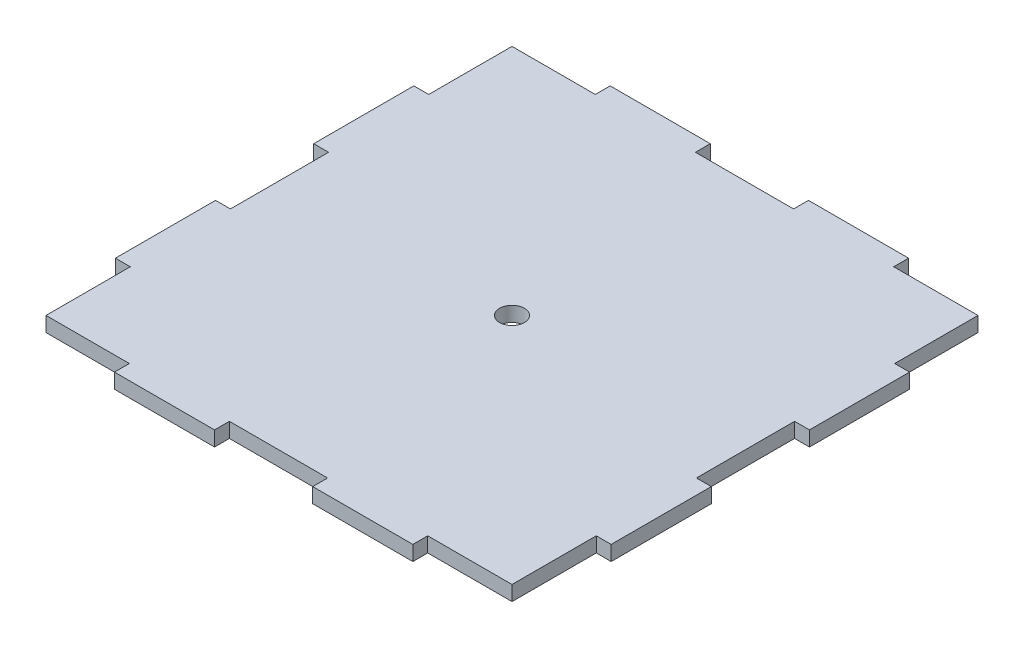
SolidWorks part; units mm, degrees
ref_plane "Front Plane" through (0, 0, 0) normal (0, 0, 1) x (1, 0, 0)
ref_plane "Top Plane" through (0, 0, 0) normal (0, 1, 0) x (1, 0, 0)
ref_plane "Right Plane" through (0, 0, 0) normal (1, 0, 0) x (0, 0, -1)
sketch "Sketch1" plane through (0, 0, 0) normal (0, 1, 0) x (1, 0, 0)
  line L0 (40, 97) -> (40, 100)
  line L1 (0, 0) -> (100, 0)
  line L2 (0, 0) -> (0, 100)
  line L3 (0, 100) -> (100, 100)
  line L4 (100, 0) -> (100, 100)
  line L9 (0, 97) -> (19.8, 97)
  line L10 (0, 97) -> (0, 100)
  line L11 (0, 100) -> (19.8, 100)
  line L12 (19.8, 97) -> (19.8, 100)
  line L13 (40, 97) -> (59.8, 97)
  line L14 (59.8, 97) -> (59.8, 100)
  line L15 (40, 100) -> (59.8, 100)
  line L16 (80, 97) -> (80, 100)
  line L17 (80, 97) -> (99.8, 97)
  line L18 (99.8, 97) -> (99.8, 100)
  line L19 (80, 100) -> (99.8, 100)
  line L20 (3, 60) -> (3, 40.2)
  line L21 (3, 100) -> (0, 100)
  line L22 (3, 100) -> (3, 80.2)
  line L23 (3, 80.2) -> (0, 80.2)
  line L24 (0, 100) -> (0, 80.2)
  line L25 (3, 60) -> (0, 60)
  line L26 (0, 60) -> (0, 40.2)
  line L27 (3, 40.2) -> (0, 40.2)
  line L28 (3, 20) -> (3, 0.2)
  line L29 (3, 20) -> (0, 20)
  line L30 (0, 20) -> (0, 0.2)
  line L31 (3, 0.2) -> (0, 0.2)
  line L32 (-900, 50) -> (49100, 50) construction
  line L33 (50, -900) -> (50, 49100) construction
  line L34 (80, 3) -> (99.8, 3)
  line L35 (99.8, 3) -> (99.8, 0)
  line L36 (80, 0) -> (99.8, 0)
  line L37 (80, 3) -> (80, 0)
  line L38 (40, 3) -> (59.8, 3)
  line L39 (59.8, 3) -> (59.8, 0)
  line L40 (40, 0) -> (59.8, 0)
  line L41 (40, 3) -> (40, 0)
  line L42 (0, 0) -> (19.8, 0)
  line L43 (19.8, 3) -> (19.8, 0)
  line L44 (0, 3) -> (19.8, 3)
  line L45 (0, 3) -> (0, 0)
  line L46 (97, 20) -> (100, 20)
  line L47 (100, 20) -> (100, 0.2)
  line L48 (97, 0.2) -> (100, 0.2)
  line L49 (97, 20) -> (97, 0.2)
  line L50 (97, 60) -> (100, 60)
  line L51 (100, 60) -> (100, 40.2)
  line L52 (97, 40.2) -> (100, 40.2)
  line L53 (97, 60) -> (97, 40.2)
  line L54 (97, 80.2) -> (100, 80.2)
  line L55 (100, 100) -> (100, 80.2)
  line L56 (97, 100) -> (100, 100)
  line L57 (97, 100) -> (97, 80.2)
  circle A0 centre (50, 50) radius 2.5
  point P30 (100, 50)
  point P33 (50, 100)
  dimension "D11" = 5
  dimension "D1" = 100
  dimension "D2" = 100
  dimension "D3" = 19.8
  dimension "D4" = 3
  dimension "D6" = 20.2
  dimension "D7" = 19.8
  dimension "D8" = 3
  dimension "D10" = 20.2
  dimension "D5" = 3
  dimension "D9" = 3
extrude "Boss-Extrude1" add sketch "Sketch1" along normal blind 3 contours L57 L17 L16 L3 L14 L13 L0 L12 L9 L22 L23 L2 L25 L20 L27 L29 L28 L44 L43 L1 L41 L38 L39 L37 L34 L49 L46 L4 L52 L53 L50 L54
